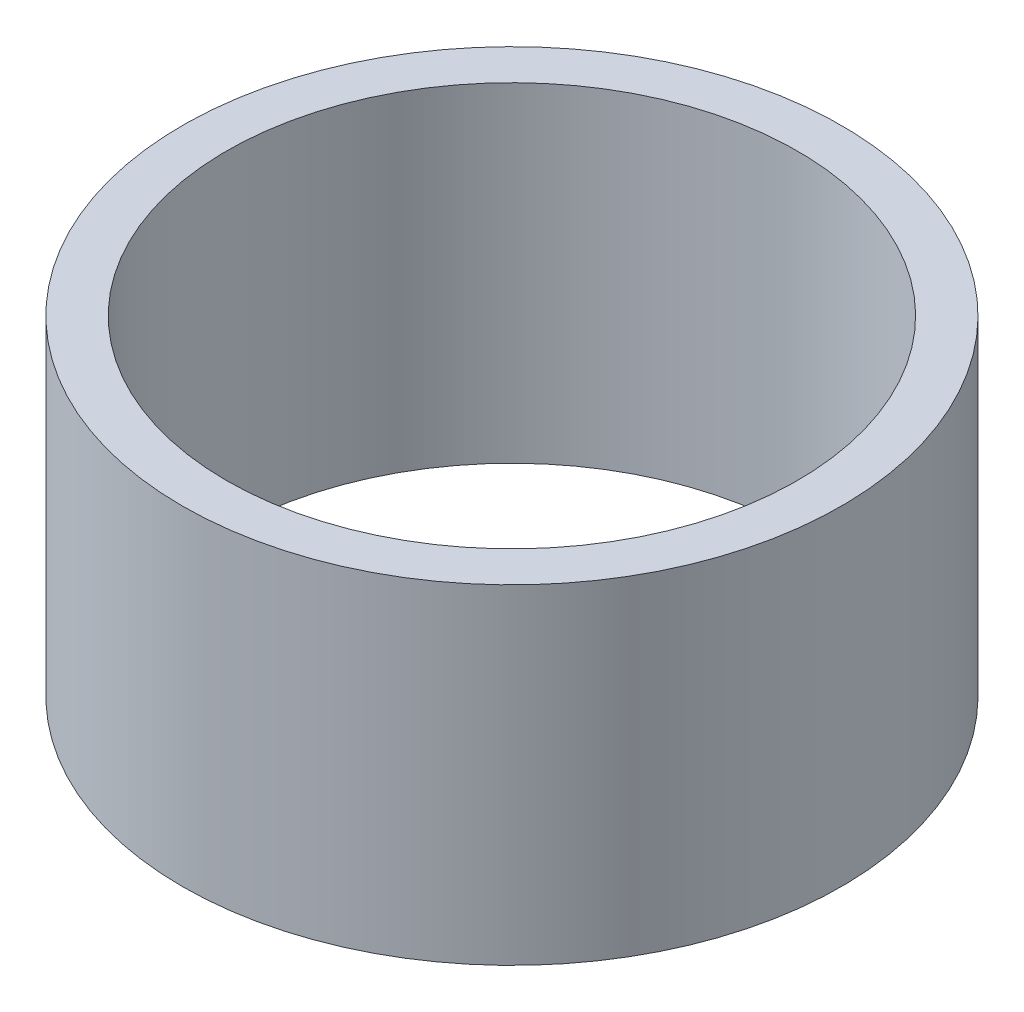
SolidWorks part; units mm, degrees
ref_plane "Front Plane" through (0, 0, 0) normal (0, 0, 1) x (1, 0, 0)
ref_plane "Top Plane" through (0, 0, 0) normal (0, 1, 0) x (1, 0, 0)
ref_plane "Right Plane" through (0, 0, 0) normal (1, 0, 0) x (0, 0, -1)
sketch "Sketch1" plane through (0, 0, 0) normal (0, 1, 0) x (1, 0, 0)
  circle A0 centre (0, 0) radius 12.7
  circle A1 centre (0, 0) radius 11
  dimension "D1" = 25.4
  dimension "D2" = 22
extrude "Boss-Extrude1" add sketch "Sketch1" along normal blind 12.7
